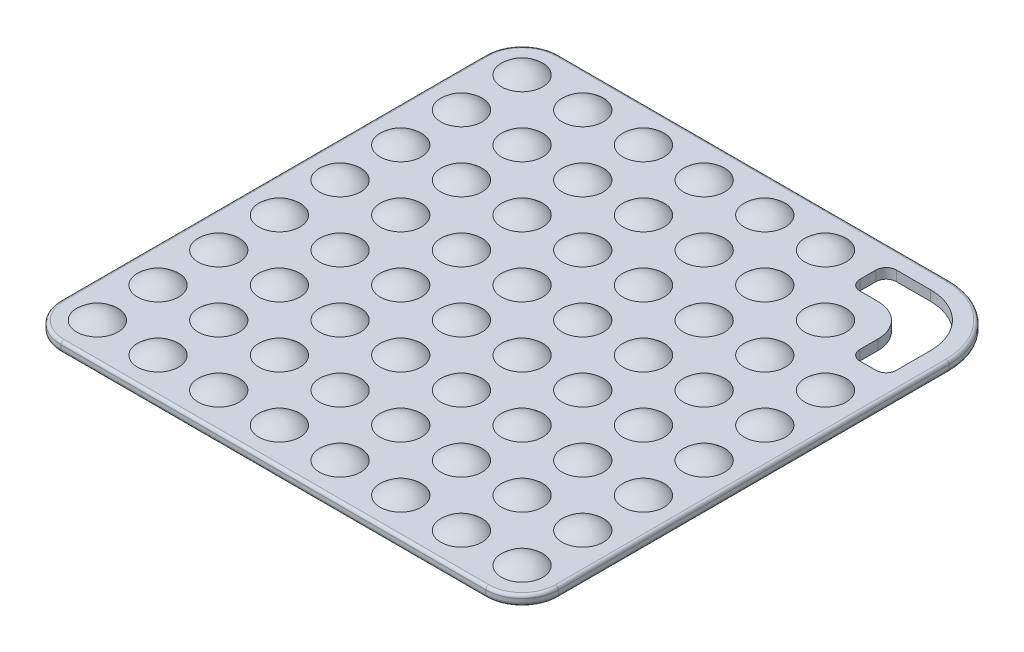
SolidWorks part; units mm, degrees
ref_plane "Front Plane" through (0, 0, 0) normal (0, 0, 1) x (1, 0, 0)
ref_plane "Top Plane" through (0, 0, 0) normal (0, 1, 0) x (1, 0, 0)
ref_plane "Right Plane" through (0, 0, 0) normal (1, 0, 0) x (0, 0, -1)
sketch "Sketch1" plane through (0, 0, 0) normal (0, 1, 0) x (1, 0, 0)
  line L0 (88, 114) -> (71, 114)
  line L1 (-105, -123) -> (105, -123)
  line L2 (-123, -105) -> (-123, 105)
  line L3 (-105, 123) -> (88, 123)
  line L4 (123, -105) -> (123, 88)
  line L5 (-123, -123) -> (123, 123) construction
  line L6 (-123, 123) -> (123, -123) construction
  line L7 (66, 109) -> (66, 101)
  line L9 (114, 88) -> (114, 71)
  line L10 (109, 66) -> (101, 66)
  line L12 (71, 96) -> (80, 96)
  line L13 (96, 80) -> (96, 71)
  arc A0 (105, -123) -> (123, -105) centre (105, -105) ccw
  arc A1 (-105, -123) -> (-123, -105) centre (-105, -105) cw
  arc A2 (-123, 105) -> (-105, 123) centre (-105, 105) cw
  arc A3 (88, 123) -> (123, 88) centre (88, 88) cw
  arc A4 (114, 88) -> (88, 114) centre (88, 88) ccw
  arc A5 (96, 80) -> (80, 96) centre (80, 80) ccw
  arc A6 (66, 101) -> (71, 96) centre (71, 101) ccw
  arc A7 (71, 114) -> (66, 109) centre (71, 109) ccw
  arc A8 (114, 71) -> (109, 66) centre (109, 71) cw
  arc A9 (101, 66) -> (96, 71) centre (101, 71) cw
  point P0 (0, 0)
  point P29 (66, 96)
  point P34 (66, 114)
  dimension "D3" = 18
  dimension "D4" = 18
  dimension "D5" = 52
  dimension "D7" = 32
  dimension "D8" = 5
  dimension "D9" = 35
  dimension "D1" = 246
  dimension "D2" = 246
  dimension "D6" = 22
extrude "Boss-Extrude1" add sketch "Sketch1" along normal blind 5
fillet "Fillet1" radius 1.5 16 edges at (0, 0, 123) (-117.7279, 0, 117.7279) (-123, 0, 0) (-117.7279, 0, -117.7279) (-8.5, 0, -123) (112.7487, 0, -112.7487) (123, 0, 8.5) (117.7279, 5, 117.7279) (0, 5, 123) (-117.7279, 5, 117.7279) (-123, 5, 0) (-117.7279, 5, -117.7279) (-8.5, 5, -123) (112.7487, 5, -112.7487) (117.7279, 0, 117.7279) (123, 5, 8.5)
sketch "Sketch3" plane through (0, 5, 0) normal (0, 1, 0) x (1, 0, 0)
  circle A0 centre (-105, -105) radius 8.1234 construction
  point P3 (-105, -105)
  point P5 (0, 0)
ref_plane "Plane1" through (0, 0, 105) normal (0, 0, 1) x (1, 0, 0)
sketch "Sketch4" plane through (0, 0, 105) normal (0, 0, 1) x (1, 0, 0)
  line L0 (-96.8766, 5) -> (-113.1234, 5) construction
  line L1 (-105, 9) -> (-105, 5)
  line L2 (-105, 5) -> (-115.198, 5)
  arc A0 (-105, 9) -> (-115.198, 5) centre (-105, -6) ccw
  dimension "D1" = 30
  dimension "D2" = 11
revolve "Revolve1" add sketch "Sketch4" angle 360 about L1
pattern_linear "LPattern1" count 8 spacing 30 along (1, 0, 0) count 8 spacing 30 along (0, 0, -1) skipping (6, 7), (7, 6), (7, 7) of "Revolve1"
